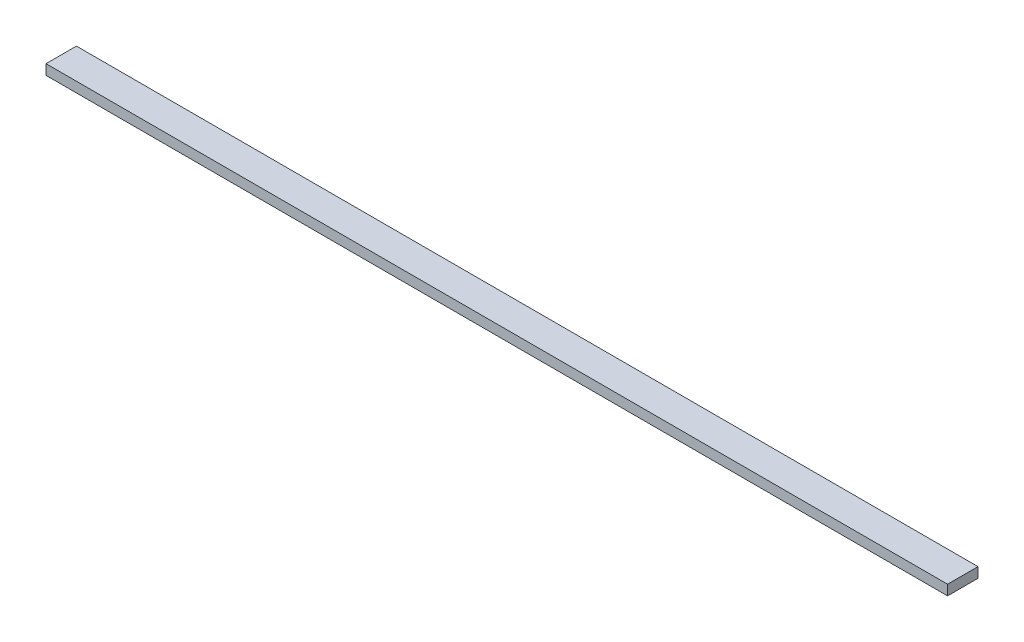
SolidWorks part; units mm, degrees
ref_plane "Front Plane" through (0, 0, 0) normal (0, 0, 1) x (1, 0, 0)
ref_plane "Top Plane" through (0, 0, 0) normal (0, 1, 0) x (1, 0, 0)
ref_plane "Right Plane" through (0, 0, 0) normal (1, 0, 0) x (0, 0, -1)
sketch "Sketch1" plane through (0, 0, 0) normal (0, 1, 0) x (1, 0, 0)
  line L0 (-444.265, 15) -> (444.265, -15) construction
  line L1 (-444.265, 15) -> (444.265, 15)
  line L2 (-444.265, 15) -> (-444.265, -15)
  line L3 (-444.265, -15) -> (444.265, -15)
  line L4 (444.265, 15) -> (444.265, -15)
  dimension "D1" = 888.53
  dimension "D2" = 30
extrude "Boss-Extrude1" add sketch "Sketch1" along normal blind 10
